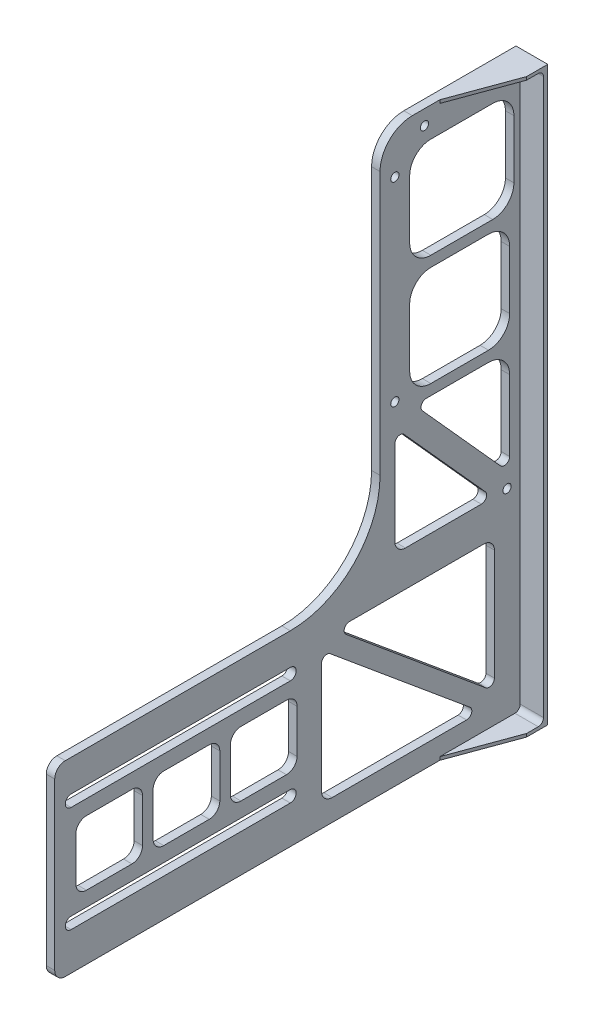
SolidWorks part; units mm, degrees
ref_plane "Front Plane" through (0, 0, 0) normal (0, 0, 1) x (1, 0, 0)
ref_plane "Top Plane" through (0, 0, 0) normal (0, 1, 0) x (1, 0, 0)
ref_plane "Right Plane" through (0, 0, 0) normal (1, 0, 0) x (0, 0, -1)
ref_plane "Plane1" through (122, 0, 0) normal (-1, 0, 0) x (0, -1, 0)
sketch "Sketch1" plane through (122, 0, 0) normal (-1, 0, 0) x (0, -1, 0)
  line L0 (42.95, 15.7375) -> (42.95, 13.2375)
  line L1 (42.95, 13.2375) -> (40.95, 11.3375)
  line L2 (40.95, 11.3375) -> (33.95, 11.3375)
  line L3 (33.95, 11.3375) -> (31.95, 13.2375)
  line L4 (31.95, 13.2375) -> (31.95, 15.7375)
  line L5 (31.95, 15.7375) -> (42.95, 15.7375)
  line L6 (30.95, 11.3375) -> (17.5, 11.3375)
  line L7 (17.5, 11.3375) -> (17.5, 13.9375)
  line L8 (30.95, 13.9375) -> (30.95, 11.3375)
  line L9 (-67.5, -1.6625) -> (202.8523, -1.6625)
  line L10 (202.8523, -1.6625) -> (202.8523, 220.3375)
  line L12 (72.1023, 66.5875) -> (-52.25, 66.5875)
  line L14 (-67.5, 51.3375) -> (-67.5, -1.6625)
  line L15 (202.8523, 220.3375) -> (114.5, 220.3375)
  line L17 (114.5, 220.3375) -> (114.5, 108.9852)
  circle A0 centre (-60.5, 6.5875) radius 1.95
  circle A1 centre (107.5, 6.5875) radius 1.95
  circle A2 centre (-60.5, 45.5875) radius 1.95
  arc A3 (17.5, 13.9375) -> (30.95, 13.9375) centre (24.225, 5.7155) cw
  circle A4 centre (-46.5, 59.5875) radius 1.95
  circle A5 centre (45.5, 59.5875) radius 1.95
  arc A6 (72.1023, 66.5875) -> (114.5, 108.9852) centre (72.1023, 108.9852) ccw
  arc A7 (-67.5, 51.3375) -> (-52.25, 66.5875) centre (-52.25, 51.3375) cw
  dimension "D6" = 7
  dimension "D1" = 7
  dimension "D2" = 21
  dimension "D3" = 7
  dimension "D5" = 60
  dimension "D7" = 7
  dimension "D8" = 175
  dimension "D9" = 21
  dimension "D10" = 60
  dimension "D11" = 270.3523
  dimension "D12" = 222
  dimension "D13" = 88.3523
  dimension "D14" = 113
extrude "Boss-Extrude1" add sketch "Sketch1" against normal blind 15
sketch "Sketch2" plane through (137, 0, 0) normal (1, 0, 0) x (0, 0, -1)
  line L0 (-42.5875, 53.5) -> (-13.3375, 53.5)
  line L3 (-42.5875, -46.5) -> (-15.3375, -46.5)
  line L4 (-55.2293, -61.015) -> (-16.8643, -103.6411)
  line L5 (-42.5875, 6) -> (-13.3375, 6)
  line L6 (-42.5875, 1) -> (-15.3375, 1)
  line L7 (-52.5875, 43.5) -> (-52.5875, 16)
  line L8 (-52.5875, -9) -> (-52.5875, -36.5)
  line L9 (-5.3375, -36.5) -> (-5.3375, -9)
  line L10 (-3.3375, 16) -> (-3.3375, 43.5)
  line L11 (1.6625, 67.5) -> (1.6625, -202.8523) construction
  line L12 (-44.7258, -51.5) -> (-15.3375, -51.5)
  line L13 (-5.3375, -61.5) -> (-5.3375, -94.9853)
  line L14 (-9.6957, -96.6577) -> (-46.584, -55.6724)
  line L15 (-18.7225, -107.8136) -> (-54.5875, -107.8136)
  line L16 (-59.5875, -102.8136) -> (-59.5875, -62.6875)
  line L18 (-66.5875, -72.1023) -> (-66.5875, 52.25) construction
  circle A0 centre (-45.5875, 60.5) radius 1.95 construction
  arc A1 (-16.8643, -103.6411) -> (-18.7225, -107.8136) centre (-18.7225, -105.3136) cw
  circle A2 centre (-59.5875, 46.5) radius 1.95 construction
  circle A3 centre (-59.5875, -45.5) radius 1.95 construction
  arc A4 (-5.3375, -36.5) -> (-15.3375, -46.5) centre (-15.3375, -36.5) cw
  arc A5 (-52.5875, -36.5) -> (-42.5875, -46.5) centre (-42.5875, -36.5) ccw
  arc A6 (-52.5875, 43.5) -> (-42.5875, 53.5) centre (-42.5875, 43.5) cw
  arc A7 (-13.3375, 53.5) -> (-3.3375, 43.5) centre (-13.3375, 43.5) cw
  arc A8 (-15.3375, 1) -> (-5.3375, -9) centre (-15.3375, -9) cw
  arc A9 (-13.3375, 6) -> (-3.3375, 16) centre (-13.3375, 16) ccw
  arc A10 (-42.5875, 6) -> (-52.5875, 16) centre (-42.5875, 16) cw
  arc A11 (-42.5875, 1) -> (-52.5875, -9) centre (-42.5875, -9) ccw
  arc A12 (-5.3375, -94.9853) -> (-9.6957, -96.6577) centre (-7.8375, -94.9853) cw
  arc A13 (-44.7258, -51.5) -> (-46.584, -55.6724) centre (-44.7258, -54) ccw
  arc A14 (-15.3375, -51.5) -> (-5.3375, -61.5) centre (-15.3375, -61.5) cw
  arc A15 (-55.2293, -61.015) -> (-59.5875, -62.6875) centre (-57.0875, -62.6875) ccw
  arc A16 (-54.5875, -107.8136) -> (-59.5875, -102.8136) centre (-54.5875, -102.8136) cw
  point P39 (-5.3375, -101.5)
  point P44 (-5.3375, -51.5)
  dimension "D7" = 7
  dimension "D8" = 10
  dimension "D12" = 2.5
  dimension "D13" = 10
  dimension "D16" = 2.5
  dimension "D17" = 5
  dimension "D1" = 7
  dimension "D2" = 5
  dimension "D3" = 7
  dimension "D4" = 100
  dimension "D5" = 47.5
  dimension "D6" = 47.5
  dimension "D9" = 7
  dimension "D10" = 5
  dimension "D11" = 50
  dimension "D14" = 7
  dimension "D15" = 10
extrude "Cut-Extrude2" cut sketch "Sketch2" against normal through all
sketch "Sketch3" plane through (137, 0, 0) normal (1, 0, 0) x (0, 0, -1)
  line L0 (-212.5875, -132.25) -> (-108.9852, -132.25) construction
  line L1 (-212.5875, -129.5) -> (-108.9852, -129.5)
  line L2 (-212.5875, -135) -> (-108.9852, -135)
  line L3 (-220.3375, -202.8523) -> (-220.3375, -114.5) construction
  line L4 (-220.3375, -114.5) -> (-108.9852, -114.5) construction
  line L6 (-212.5875, -182.25) -> (-108.9852, -182.25) construction
  line L7 (-212.5875, -179.5) -> (-108.9852, -179.5)
  line L8 (-212.5875, -185) -> (-108.9852, -185)
  arc A0 (-212.5875, -129.5) -> (-212.5875, -135) centre (-212.5875, -132.25) ccw
  arc A1 (-108.9852, -135) -> (-108.9852, -129.5) centre (-108.9852, -132.25) ccw
  arc A2 (-212.5875, -179.5) -> (-212.5875, -185) centre (-212.5875, -182.25) ccw
  arc A3 (-108.9852, -185) -> (-108.9852, -179.5) centre (-108.9852, -182.25) ccw
  point P2 (-160.7864, -132.25)
  point P7 (-215.3375, -132.25)
  point P17 (-160.7864, -182.25)
  dimension "D4" = 0
  dimension "D1" = 5.5
  dimension "D2" = 5
  dimension "D3" = 15
  dimension "D5" = 2
  dimension "D6" = 50
extrude "Cut-Extrude3" cut sketch "Sketch3" against normal through all
sketch "Sketch4" plane through (137, 0, 0) normal (1, 0, 0) x (0, 0, -1)
  line L3 (-220.3375, -158.6761) -> (1.6625, -158.6761) construction
  line L9 (-220.3375, -202.8523) -> (-220.3375, -114.5) construction
  line L47 (1.6625, 67.5) -> (1.6625, -202.8523) construction
  line L67 (-94.2352, -192.6426) -> (-12.5471, -124.7096) construction
  line L68 (-94.2352, -124.7096) -> (-12.5471, -192.6426) construction
  line L69 (-94.2352, -187.6426) -> (-94.2352, -135.2426)
  line L70 (-90.1367, -133.3204) -> (-24.1205, -188.2205)
  line L71 (-25.719, -192.6426) -> (-89.2352, -192.6426)
  line L72 (-12.5471, -129.7096) -> (-12.5471, -182.1096)
  line L73 (-16.6456, -184.0318) -> (-82.6618, -129.1318)
  line L74 (-81.0633, -124.7096) -> (-17.5471, -124.7096)
  arc A19 (-12.5471, -129.7096) -> (-17.5471, -124.7096) centre (-17.5471, -129.7096) ccw
  arc A20 (-89.2352, -192.6426) -> (-94.2352, -187.6426) centre (-89.2352, -187.6426) cw
  arc A21 (-24.1205, -188.2205) -> (-25.719, -192.6426) centre (-25.719, -190.1426) cw
  arc A22 (-82.6618, -129.1318) -> (-81.0633, -124.7096) centre (-81.0633, -127.2096) cw
  arc A23 (-12.5471, -182.1096) -> (-16.6456, -184.0318) centre (-15.0471, -182.1096) cw
  arc A24 (-94.2352, -135.2426) -> (-90.1367, -133.3204) centre (-91.7352, -135.2426) cw
  point P6 (-53.3912, -158.6761)
  dimension "D2" = 2.5
  dimension "D4" = 4
  dimension "D5" = 4
  dimension "D1" = 5
extrude "Cut-Extrude4" cut sketch "Sketch4" against normal through all
sketch "Sketch5" plane through (137, 0, 0) normal (1, 0, 0) x (0, 0, -1)
  line L0 (-210.3375, -147) -> (-210.3375, -167.5)
  line L1 (-205.3375, -142) -> (-183.8303, -142)
  line L2 (-205.3375, -172.5) -> (-183.8303, -172.5)
  line L3 (-178.8303, -147) -> (-178.8303, -167.5)
  line L4 (-173.8303, -147) -> (-173.8303, -167.5)
  line L5 (-168.8303, -142) -> (-147.3231, -142)
  line L6 (-168.8303, -172.5) -> (-147.3231, -172.5)
  line L7 (-142.3231, -147) -> (-142.3231, -167.5)
  line L8 (-137.3231, -147) -> (-137.3231, -167.5)
  line L9 (-132.3231, -142) -> (-110.816, -142)
  line L10 (-132.3231, -172.5) -> (-110.816, -172.5)
  line L11 (-105.816, -147) -> (-105.816, -167.5)
  line L12 (-220.3375, -202.8523) -> (-220.3375, -114.5) construction
  line L14 (-212.5875, -135) -> (-108.9852, -135) construction
  line L16 (-108.9852, -179.5) -> (-212.5875, -179.5) construction
  arc A0 (-147.3231, -142) -> (-142.3231, -147) centre (-147.3231, -147) cw
  arc A1 (-132.3231, -142) -> (-137.3231, -147) centre (-132.3231, -147) ccw
  arc A2 (-110.816, -142) -> (-105.816, -147) centre (-110.816, -147) cw
  arc A3 (-110.816, -172.5) -> (-105.816, -167.5) centre (-110.816, -167.5) ccw
  arc A4 (-137.3231, -167.5) -> (-132.3231, -172.5) centre (-132.3231, -167.5) ccw
  arc A5 (-147.3231, -172.5) -> (-142.3231, -167.5) centre (-147.3231, -167.5) ccw
  arc A6 (-173.8303, -167.5) -> (-168.8303, -172.5) centre (-168.8303, -167.5) ccw
  arc A7 (-168.8303, -142) -> (-173.8303, -147) centre (-168.8303, -147) ccw
  arc A8 (-183.8303, -142) -> (-178.8303, -147) centre (-183.8303, -147) cw
  arc A9 (-183.8303, -172.5) -> (-178.8303, -167.5) centre (-183.8303, -167.5) ccw
  arc A10 (-210.3375, -167.5) -> (-205.3375, -172.5) centre (-205.3375, -167.5) ccw
  arc A11 (-205.3375, -142) -> (-210.3375, -147) centre (-205.3375, -147) ccw
  dimension "D7" = 5
  dimension "D1" = 10
  dimension "D3" = 5
  dimension "D4" = 5
  dimension "D5" = 7
  dimension "D6" = 7
extrude "Cut-Extrude5" cut sketch "Sketch5" against normal through all
fillet "Fillet1" radius 5 2 edges at (129.5, -202.8523, 220.3375) (129.5, -114.5, 220.3375)
sketch "Sketch7" plane through (137, 0, 0) normal (1, 0, 0) x (0, 0, -1)
  line L0 (-0.3375, 66) -> (-0.3375, -201.3523)
  line L1 (-0.3375, 66) -> (-220.3375, 66)
  line L2 (-0.3375, -201.3523) -> (-220.3375, -201.3523)
  line L3 (-220.3375, 66) -> (-220.3375, -201.3523)
  line L5 (-220.3375, -197.8523) -> (-220.3375, -119.5) construction
  line L6 (-51.3375, 67.5) -> (1.6625, 67.5) construction
  line L7 (1.6625, -202.8523) -> (-215.3375, -202.8523) construction
  line L8 (1.6625, 67.5) -> (1.6625, -202.8523) construction
  point P6 (-220.3375, -196.1073)
  dimension "D1" = 1.5
  dimension "D2" = 1.5
  dimension "D3" = 2
extrude "Cut-Extrude6" cut sketch "Sketch7" against normal blind 11
sketch "Sketch8" plane through (0, -202.8523, 0) normal (0, -1, 0) x (1, 0, 0)
  line L0 (137, 54.3532) -> (137, 242.4437)
  line L2 (137, 242.4437) -> (126, 242.4437)
  line L3 (126, 38.3375) -> (126, 242.4437)
  line L4 (137, -1.6625) -> (137, 215.3375) construction
  line L5 (126, 38.3375) -> (137, 8.3375)
  line L6 (137, 8.3375) -> (137, 54.3532)
  line L7 (137, -1.6625) -> (122, -1.6625) construction
  line L8 (122, -1.6625) -> (122, 215.3375) construction
  dimension "D1" = 10
  dimension "D2" = 40
  dimension "D3" = 4
extrude "Cut-Extrude7" cut sketch "Sketch8" against normal through all
fillet "Fillet2" radius 2.5 2 edges at (131.5, 66, 0.3375) (131.5, -201.3523, 0.3375)
